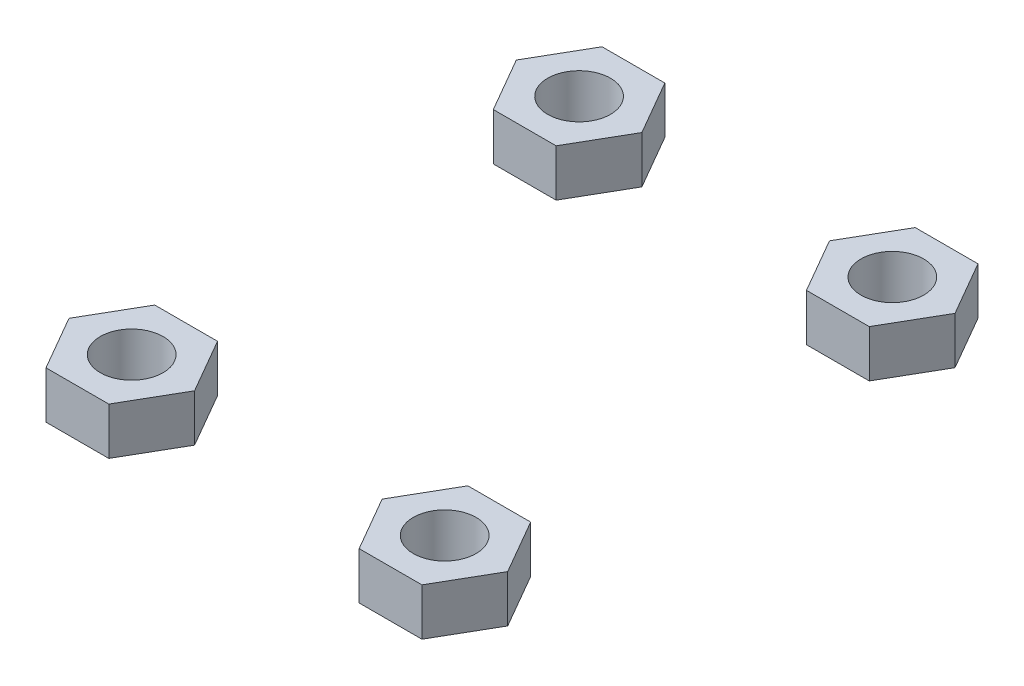
SolidWorks part; units mm, degrees
material "ASTM A36 Steel"
ref_plane "Front Plane" through (0, 0, 0) normal (0, 0, 1) x (1, 0, 0)
ref_plane "Top Plane" through (0, 0, 0) normal (0, 1, 0) x (1, 0, 0)
ref_plane "Right Plane" through (0, 0, 0) normal (1, 0, 0) x (0, 0, -1)
sketch "Sketch1" plane through (0, 0, 0) normal (0, 1, 0) x (1, 0, 0)
  line L0 (19.9503, -28.4985) -> (91.9989, -28.4985) construction
  line L1 (8, 0) -> (4, 6.9282)
  line L2 (4, 6.9282) -> (-4, 6.9282)
  line L3 (-4, 6.9282) -> (-8, 0)
  line L4 (-8, 0) -> (-4, -6.9282)
  line L5 (-4, -6.9282) -> (4, -6.9282)
  line L6 (4, -6.9282) -> (8, 0)
  line L7 (45.1505, 0.0135) -> (34.6505, 0.0135) construction
  line L8 (39.9005, 0.0135) -> (0, -57.0106) construction
  line L9 (4, -50.0689) -> (8, -56.9971)
  line L10 (-4, -50.0689) -> (4, -50.0689)
  line L11 (-8, -56.9971) -> (-4, -50.0689)
  line L12 (-4, -63.9253) -> (-8, -56.9971)
  line L13 (4, -63.9253) -> (-4, -63.9253)
  line L14 (8, -56.9971) -> (4, -63.9253)
  line L15 (19.9503, -6.9282) -> (19.9503, -47.8576) construction
  line L16 (31.9005, -56.9971) -> (35.9005, -63.9253)
  line L17 (35.9005, -63.9253) -> (43.9005, -63.9253)
  line L18 (43.9005, -63.9253) -> (47.9005, -56.9971)
  line L19 (47.9005, -56.9971) -> (43.9005, -50.0689)
  line L20 (43.9005, -50.0689) -> (35.9005, -50.0689)
  line L21 (35.9005, -50.0689) -> (31.9005, -56.9971)
  line L22 (35.9005, -6.9282) -> (31.9005, 0)
  line L23 (43.9005, -6.9282) -> (35.9005, -6.9282)
  line L24 (47.9005, 0) -> (43.9005, -6.9282)
  line L25 (43.9005, 6.9282) -> (47.9005, 0)
  line L26 (35.9005, 6.9282) -> (43.9005, 6.9282)
  line L27 (31.9005, 0) -> (35.9005, 6.9282)
  circle A0 centre (0, 0) radius 4
  circle A1 centre (0, 0) radius 6.9282 construction
  circle A2 centre (19.9503, -28.4985) radius 11 construction
  circle A3 centre (39.9005, 0.0135) radius 4
  circle A4 centre (0, 0) radius 4
  circle A5 centre (39.9005, -57.0242) radius 4
  circle A6 centre (0, -57.0106) radius 4
  dimension "D1" = 8
  dimension "D2" = 16
extrude "Boss-Extrude1" add sketch "Sketch1" along normal blind 6 contours L5 L6 L1 L2 L3 L4 A0 | L27 L22 L23 L24 L25 L26 A3 | L14 L9 L10 L11 L12 L13 A6 | L20 L21 L16 L17 L18 L19 A5
